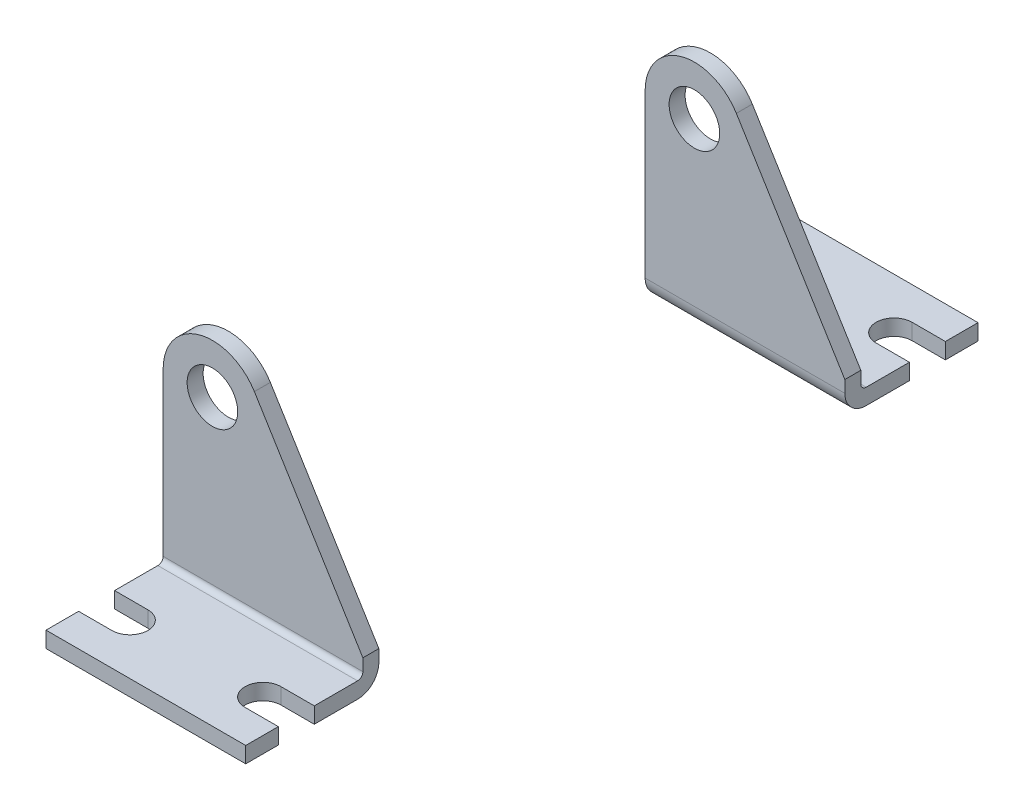
SolidWorks part; units mm, degrees
material "Galvanized Steel"
ref_plane "Front Plane" through (0, 0, 0) normal (0, 0, 1) x (1, 0, 0)
ref_plane "Top Plane" through (0, 0, 0) normal (0, 1, 0) x (1, 0, 0)
ref_plane "Right Plane" through (0, 0, 0) normal (1, 0, 0) x (0, 0, -1)
sketch "Sketch1" plane through (0, 0, 0) normal (0, 0, 1) x (1, 0, 0)
  line L0 (-9.398, 0) -> (-9.398, -35.052)
  line L1 (-9.398, -35.052) -> (28.702, -35.052)
  line L2 (28.702, -35.052) -> (28.702, -28.702)
  line L3 (28.702, -28.702) -> (8.0034, 4.9262)
  line L4 (-9.398, -32.004) -> (28.702, -32.004) construction
  circle A0 centre (0, 0) radius 4.826
  arc A1 (8.0034, 4.9262) -> (-9.398, 0) centre (0, 0) ccw
  point P9 (0, 4.826)
  dimension "Hole" = 9.652
  dimension "Height" = 44.45
  dimension "Vert Height" = 6.35
  dimension "Width" = 38.1
  dimension "Thickness" = 3.048
  dimension "Vert Hole" = 35.052
sketch "Sketch2" plane through (0, 0, 0) normal (0, 1, 0) x (1, 0, 0)
  line L0 (-9.398, -15.748) -> (28.702, -15.748) construction
  line L1 (-9.398, -25.4) -> (28.702, -25.4)
  line L2 (-9.398, -25.4) -> (-9.398, 0)
  line L3 (-9.398, 0) -> (28.702, 0)
  line L4 (28.702, -25.4) -> (28.702, 0)
  line L5 (-3.048, -19.177) -> (-9.398, -19.177)
  line L6 (-3.048, -12.319) -> (-9.398, -12.319)
  line L7 (22.352, -12.319) -> (28.702, -12.319)
  line L8 (22.352, -19.177) -> (28.702, -19.177)
  arc A0 (-3.048, -19.177) -> (-3.048, -12.319) centre (-3.048, -15.748) ccw
  arc A1 (22.352, -12.319) -> (22.352, -19.177) centre (22.352, -15.748) ccw
  dimension "Depth" = 25.4
  dimension "Hole Offset" = 15.748
  dimension "Hole Location" = 25.4
  dimension "Hole Size" = 6.858
sketch "Sketch3" plane through (0, 0, 0) normal (0, 0, 1) x (1, 0, 0)
  line L0 (-9.398, 0) -> (-9.398, -35.052) construction
  line L1 (28.702, -28.702) -> (8.0034, 4.9262) construction
  line L2 (28.702, -35.052) -> (28.702, -28.702) construction
  line L3 (-9.398, -35.052) -> (28.702, -35.052) construction
  line L4 (-9.398, 0) -> (-9.398, -35.052)
  line L5 (28.702, -28.702) -> (8.0034, 4.9262)
  line L6 (28.702, -35.052) -> (28.702, -28.702)
  line L7 (-9.398, -35.052) -> (28.702, -35.052)
  arc A0 (8.0034, 4.9262) -> (-9.398, 0) centre (0, 0) ccw construction
  circle A1 centre (0, 0) radius 4.826 construction
  arc A2 (8.0034, 4.9262) -> (-9.398, 0) centre (0, 0) ccw
  circle A3 centre (0, 0) radius 4.826
extrude "Boss-Extrude1" add sketch "Sketch3" along normal blind 3.048
sketch "Sketch4" plane through (0, 0, 3.048) normal (0, 0, 1) x (1, 0, 0)
  line L1 (-9.398, -35.052) -> (28.702, -35.052)
  line L2 (-9.398, -35.052) -> (-9.398, -32.004)
  line L3 (-9.398, -32.004) -> (28.702, -32.004)
  line L4 (28.702, -35.052) -> (28.702, -32.004)
extrude "Boss-Extrude2" add sketch "Sketch4" along normal up to vertex (22.352 mm away) up to point (-9.398, 0, 25.4)
sketch "Sketch5" plane through (0, -32.004, 0) normal (0, 1, 0) x (1, 0, 0)
  line L0 (-3.048, -19.177) -> (-9.398, -19.177) construction
  line L1 (-3.048, -12.319) -> (-9.398, -12.319) construction
  line L2 (22.352, -12.319) -> (28.702, -12.319) construction
  line L3 (22.352, -19.177) -> (28.702, -19.177) construction
  line L4 (-3.048, -19.177) -> (-9.398, -19.177)
  line L5 (-3.048, -12.319) -> (-9.398, -12.319)
  line L6 (22.352, -12.319) -> (28.702, -12.319)
  line L7 (22.352, -19.177) -> (28.702, -19.177)
  line L8 (-9.398, -19.177) -> (-9.398, -12.319)
  line L9 (28.702, -19.177) -> (28.702, -12.319)
  arc A0 (-3.048, -19.177) -> (-3.048, -12.319) centre (-3.048, -15.748) ccw construction
  arc A1 (22.352, -12.319) -> (22.352, -19.177) centre (22.352, -15.748) ccw construction
  arc A2 (-3.048, -19.177) -> (-3.048, -12.319) centre (-3.048, -15.748) ccw
  arc A3 (22.352, -12.319) -> (22.352, -19.177) centre (22.352, -15.748) ccw
extrude "Cut-Extrude1" cut sketch "Sketch5" against normal through all
fillet "Fillet1" radius 1.016 1 edges
fillet "Fillet2" radius 4.064 1 edges at (9.652, -35.052, 0)
ref_plane "Plane1" through (0, 0, -44.45) normal (0, 0, 1) x (1, 0, 0)
mirror "Mirror2" about plane through (0, 0, -44.45) normal (0, 0, 1) of bodies 103
sketch "Sketch8" plane through (0, 0, -91.948) normal (0, 0, -1) x (-1, 0, 0)
  line L0 (0, 4.826) -> (0, -4.826) construction
  circle A0 centre (0, 0) radius 4.826 construction
equation "\"D1@Boss-Extrude1\" = \"Thickness@Sketch1\""
equation "\"D1@Fillet1\" = \"Thickness@Sketch1\"/3"
equation "\"D1@Fillet2\" = \"Thickness@Sketch1\"+\"D1@Fillet1\""
